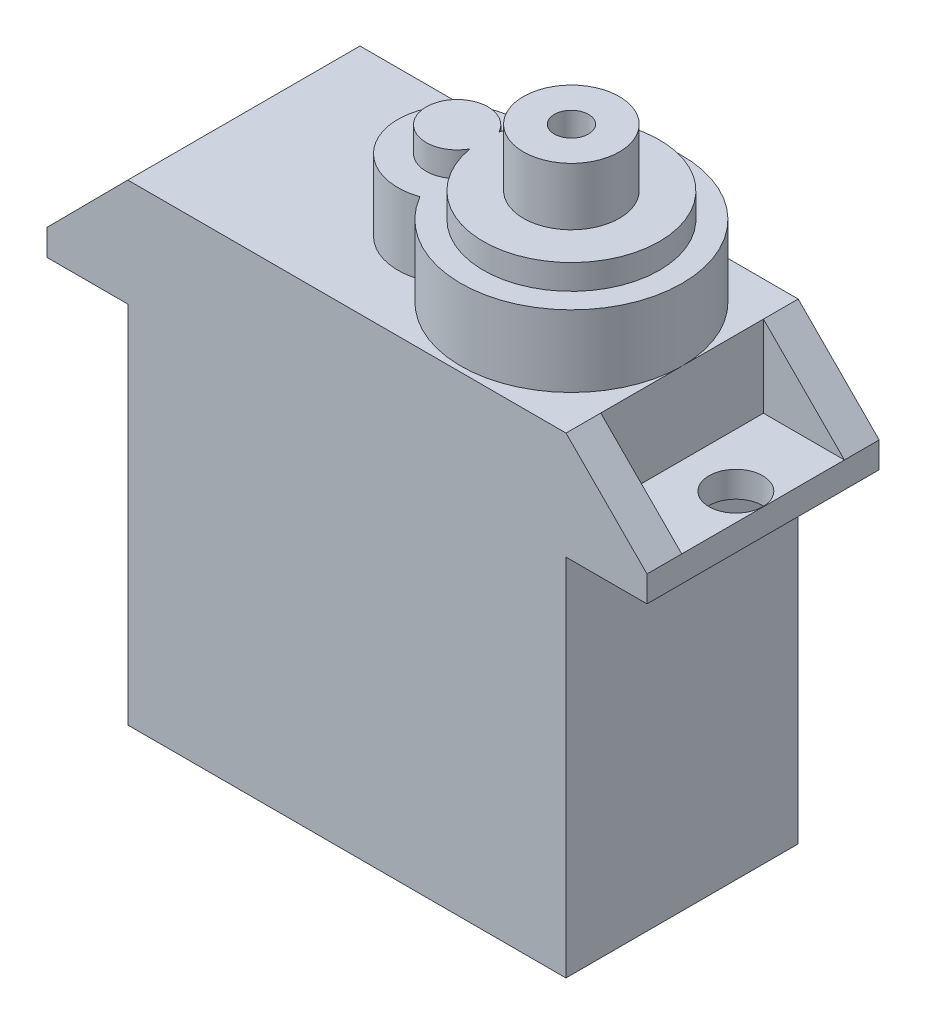
SolidWorks part; units mm, degrees
ref_plane "Front" through (0, 0, 0) normal (0, 0, 1) x (1, 0, 0)
ref_plane "Top" through (0, 0, 0) normal (0, 1, 0) x (1, 0, 0)
ref_plane "Right" through (0, 0, 0) normal (1, 0, 0) x (0, 0, -1)
sketch "Sketch2" plane through (0, 0, 0) normal (0, 1, 0) x (1, 0, 0)
  line L1 (-11.415, 6.05) -> (11.415, 6.05)
  line L2 (-11.415, 6.05) -> (-11.415, -6.05)
  line L3 (-11.415, -6.05) -> (11.415, -6.05)
  line L4 (11.415, 6.05) -> (11.415, -6.05)
  line L5 (-11.415, 6.05) -> (11.415, -6.05) construction
  line L6 (-11.415, -6.05) -> (11.415, 6.05) construction
  point P0 (0, 0)
  dimension "D1" = 22.83
  dimension "D2" = 12.1
extrude "Boss-Extrude1" add sketch "Sketch2" along normal blind 19
sketch "Sketch3" plane through (0, 19, 0) normal (0, 1, 0) x (1, 0, 0)
  line L0 (11.415, 6.05) -> (-11.415, 6.05) construction
  line L1 (-15.64, 6.05) -> (15.64, 6.05)
  line L2 (-15.64, 6.05) -> (-15.64, -6.05)
  line L3 (-15.64, -6.05) -> (15.64, -6.05)
  line L4 (15.64, 6.05) -> (15.64, -6.05)
  line L5 (-15.64, 6.05) -> (15.64, -6.05) construction
  line L6 (-15.64, -6.05) -> (15.64, 6.05) construction
  point P0 (0, 0)
  dimension "D1" = 31.28
extrude "Boss-Extrude2" add sketch "Sketch3" along normal blind 5.6
sketch "Sketch4" plane through (0, 24.6, 0) normal (0, 1, 0) x (1, 0, 0)
  line L0 (-15.64, -6.05) -> (15.64, -6.05) construction
  line L1 (-11.42, 6.05) -> (11.42, 6.05)
  line L2 (-11.42, 6.05) -> (-11.42, -6.05)
  line L3 (-11.42, -6.05) -> (11.42, -6.05)
  line L4 (11.42, 6.05) -> (11.42, -6.05)
  line L5 (-11.42, 6.05) -> (11.42, -6.05) construction
  line L6 (-11.42, -6.05) -> (11.42, 6.05) construction
  point P0 (0, 0)
  dimension "D1" = 22.84
sketch "Sketch5" plane through (0, 0, 6.05) normal (0, 0, 1) x (1, 0, 0)
  line L0 (-15.64, 20.35) -> (-11.42, 24.6)
  line L1 (-15.64, 24.6) -> (-15.64, 19) construction
  line L2 (-11.42, 24.6) -> (11.42, 24.6) construction
  line L3 (-11.42, 24.6) -> (11.42, 24.6) construction
  line L4 (-11.42, 24.6) -> (-15.64, 24.6)
  line L5 (-15.64, 24.6) -> (-15.64, 20.35)
  line L6 (-15.64, 19) -> (-11.415, 19) construction
  line L7 (0, 24.6) -> (0, 11.5294) construction
  line L8 (-11.42, 24.6) -> (11.42, 24.6) construction
  line L9 (15.64, 24.6) -> (15.64, 20.35)
  line L10 (11.42, 24.6) -> (15.64, 24.6)
  line L11 (15.64, 20.35) -> (11.42, 24.6)
  dimension "D1" = 1.35
extrude "Cut-Extrude1" cut sketch "Sketch5" against normal through all
sketch "Sketch6" plane through (0, 24.6, 0) normal (0, 1, 0) x (1, 0, 0)
  line L0 (0, 8.7879) -> (0, -9.3434) construction
  line L1 (-18.1313, 0) -> (20.22, 0) construction
  line L2 (11.42, 6.05) -> (11.42, -6.05) construction
  line L3 (15.64, 4.24) -> (11.42, 4.24)
  line L4 (15.64, 4.24) -> (15.64, -4.24)
  line L5 (15.64, -4.24) -> (11.42, -4.24)
  line L6 (11.42, 4.24) -> (11.42, -4.24)
  line L7 (15.64, 4.24) -> (11.42, -4.24) construction
  line L8 (15.64, -4.24) -> (11.42, 4.24) construction
  line L9 (15.64, 6.05) -> (15.64, -6.05) construction
  line L10 (-15.64, -4.24) -> (-11.42, 4.24) construction
  line L11 (-15.64, 4.24) -> (-11.42, -4.24) construction
  line L12 (-11.42, 4.24) -> (-11.42, -4.24)
  line L13 (-15.64, -4.24) -> (-11.42, -4.24)
  line L14 (-15.64, 4.24) -> (-15.64, -4.24)
  line L15 (-15.64, 4.24) -> (-11.42, 4.24)
  point P5 (13.53, 0)
  point P18 (-13.53, 0)
  dimension "D1" = 8.48
extrude "Cut-Extrude2" cut sketch "Sketch6" against normal offset from surface (4.25 mm away) 1.35 up to face at (13.5275, 19, 1.5125)
sketch "Sketch7" plane through (0, 20.35, 0) normal (0, 1, 0) x (1, 0, 0)
  line L0 (0, 8.3879) -> (0, -9.7656) construction
  circle A0 centre (14.22, 0) radius 1.4
  circle A1 centre (-14.22, 0) radius 1.4
  point P7 (-12.82, 0)
  point P8 (12.82, 0)
  dimension "D1" = 2.8
  dimension "D2" = 25.64
extrude "Cut-Extrude3" cut sketch "Sketch7" against normal up to next
sketch "Sketch8" plane through (0, 24.6, 0) normal (0, 1, 0) x (1, 0, 0)
  line L0 (11.42, 6.05) -> (11.42, -6.05) construction
  circle A0 centre (5.65, 0) radius 5.77
  circle A1 centre (-0.305, 0) radius 3.085
  point P4 (-3.39, 0)
  point P5 (11.42, 0)
  dimension "D1" = 11.54
  dimension "D2" = 6.17
  dimension "D3" = 14.81
extrude "Boss-Extrude3" add sketch "Sketch8" along normal blind 3.73 contours A0 A1 | A0 A1 | A1 A0
sketch "Sketch9" plane through (0, 28.33, 0) normal (0, 1, 0) x (1, 0, 0)
  circle A0 centre (5.65, 0) radius 4.59
  circle A1 centre (-0.305, 0) radius 1.61
  dimension "D1" = 9.18
  dimension "D2" = 3.22
extrude "Boss-Extrude4" add sketch "Sketch9" along normal blind 1.3 contours A0 A1 | A1 A0
sketch "Sketch10" plane through (0, 29.63, 0) normal (0, 1, 0) x (1, 0, 0)
  circle A0 centre (5.65, 0) radius 2.5
  dimension "D1" = 5
extrude "Boss-Extrude5" add sketch "Sketch10" along normal blind 3
sketch "Sketch12" plane through (0, 32.63, 0) normal (0, 1, 0) x (1, 0, 0)
  circle A0 centre (5.65, 0) radius 0.89
  dimension "D1" = 1.78
extrude "Cut-Extrude4" cut sketch "Sketch12" against normal blind 14
